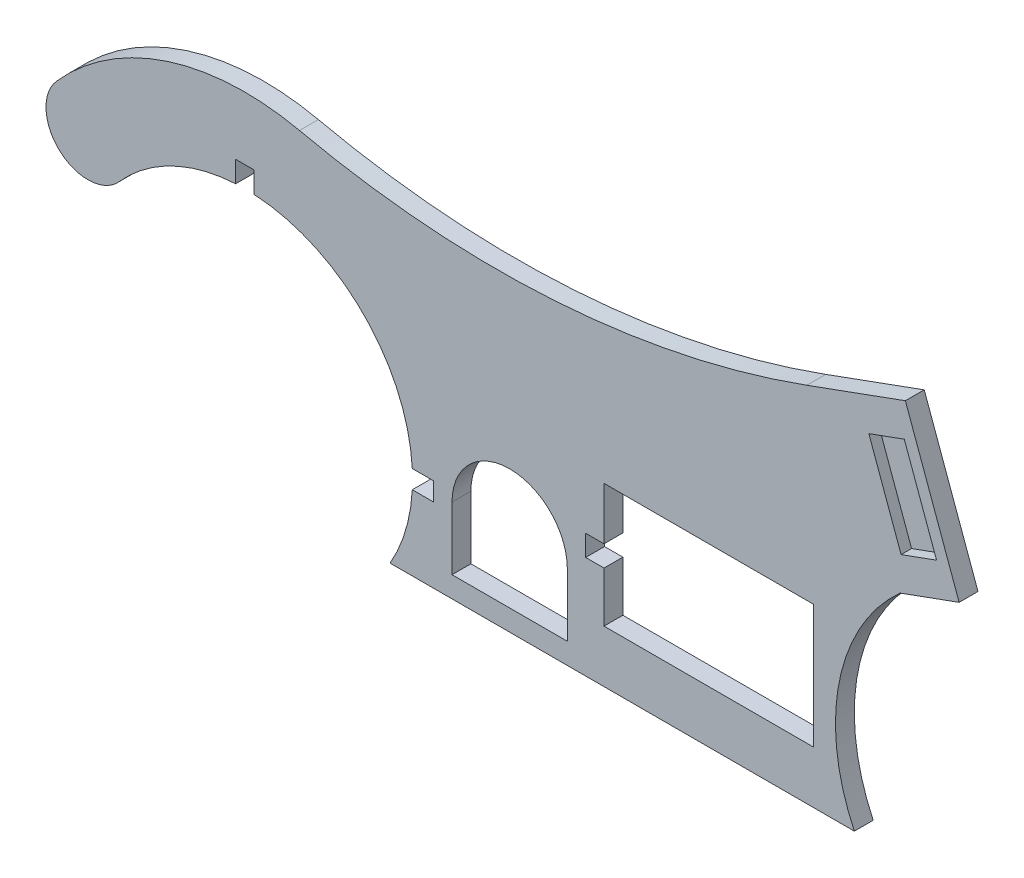
SolidWorks part; units mm, degrees
ref_plane "Спереди" through (0, 0, 0) normal (0, 0, 1) x (1, 0, 0)
ref_plane "Сверху" through (0, 0, 0) normal (0, 1, 0) x (1, 0, 0)
ref_plane "Справа" through (0, 0, 0) normal (1, 0, 0) x (0, 0, -1)
sketch "Sketch1" plane through (0, 0, 0) normal (0, 0, 1) x (1, 0, 0)
  line L0 (0, 0) -> (51.303, -140.9539)
  line L1 (-1000, 0) -> (49000, 0) construction
  line L2 (10.6418, 0) -> (119.8328, -300) construction
  line L3 (0, 0) -> (-93.9693, -34.202)
  line L4 (-491.6031, -380) -> (-48.6664, -380)
  line L5 (51.303, -140.9539) -> (-5.0785, -161.4751)
  circle A0 centre (119.8328, -300) radius 127.5 construction
  circle A1 centre (-630.1672, -300) radius 127.5 construction
  arc A3 (-491.6031, -380) -> (-749.9368, -193.9094) centre (-630.1672, -300) ccw
  arc A4 (-749.9368, -193.9094) -> (-809.8217, -140.864) centre (-779.8792, -167.3867) cw
  arc A5 (-809.8217, -140.864) -> (-578.031, -65.7313) centre (-630.1672, -300) cw
  arc A6 (-578.031, -65.7313) -> (-93.9693, -34.202) centre (-390.0044, 779.1478) ccw
  arc A7 (-48.6664, -380) -> (-5.0785, -161.4751) centre (119.8328, -300) cw
  dimension "D3" = 255
  dimension "D4" = 255
  dimension "D10" = 40
  dimension "D11" = 160
  dimension "D1" = 150
  dimension "D2" = 110
  dimension "D5" = 300
  dimension "D6" = 300
  dimension "D7" = 750
  dimension "D8" = 10
  dimension "D9" = 100
  dimension "D12" = 380
  dimension "D13" = 60
extrude "Boss-Extrude1" add sketch "Sketch1" along normal blind 18
sketch "Sketch2" plane through (0, 0, 18) normal (0, 0, 1) x (1, 0, 0)
  line L0 (-491.6031, -380) -> (-48.6664, -380) construction
  line L1 (-287.5083, -330) -> (-87.5083, -330)
  line L2 (-287.5083, -330) -> (-287.5083, -212)
  line L3 (-287.5083, -212) -> (-87.5083, -212)
  line L4 (-87.5083, -330) -> (-87.5083, -212)
  line L5 (-287.5083, -330) -> (-87.5083, -212) construction
  line L6 (-287.5083, -212) -> (-87.5083, -330) construction
  line L7 (-322.5083, -360) -> (-432.5083, -360)
  line L8 (-322.5083, -360) -> (-322.5083, -300)
  line L9 (-432.5083, -360) -> (-432.5083, -300)
  line L10 (-491.6031, -380) -> (-48.6664, -380) construction
  arc A0 (-432.5083, -300) -> (-322.5083, -300) centre (-377.5083, -300) cw
  point P0 (-187.5083, -271)
  dimension "D8" = 20
  dimension "D1" = 200
  dimension "D2" = 118
  dimension "D3" = 50
  dimension "D4" = 110
  dimension "D5" = 60
  dimension "D6" = 60
  dimension "D7" = 35
extrude "Cut-Extrude1" cut sketch "Sketch2" against normal through all
sketch "Sketch3" plane through (0, 0, 18) normal (0, 0, 1) x (1, 0, 0)
  line L0 (-1.0157, -32.295) -> (29.7661, -116.8674)
  line L1 (-1.0157, -32.295) -> (-34.8446, -44.6077)
  line L2 (29.7661, -116.8674) -> (-4.0628, -129.1801)
  line L3 (-34.8446, -44.6077) -> (-4.0628, -129.1801)
  line L5 (51.303, -140.9539) -> (0, 0) construction
  line L6 (0, 0) -> (-93.9693, -34.202) construction
  line L7 (-5.0785, -161.4751) -> (51.303, -140.9539) construction
  line L8 (-17.9302, -38.4514) -> (12.8516, -123.0237) construction
  dimension "D1" = 36
  dimension "D2" = 30
  dimension "D3" = 30
  dimension "D4" = 30
extrude "Cut-Extrude2" cut sketch "Sketch3" against normal blind 10
sketch "Sketch4" plane through (0, 0, 18) normal (0, 0, 1) x (1, 0, 0)
  line L0 (-630.1672, -300) -> (-630.1672, -12.7684) construction
  line L1 (-630.1672, -300) -> (-377.5083, -300) construction
  line L2 (-638.9172, -160) -> (-621.4172, -160)
  line L3 (-638.9172, -160) -> (-638.9172, -120)
  line L4 (-638.9172, -120) -> (-621.4172, -120)
  line L5 (-621.4172, -160) -> (-621.4172, -120)
  line L6 (-638.9172, -160) -> (-621.4172, -120) construction
  line L7 (-638.9172, -120) -> (-621.4172, -160) construction
  line L9 (-490.1672, -308.75) -> (-450.1672, -308.75)
  line L10 (-490.1672, -308.75) -> (-490.1672, -291.25)
  line L11 (-490.1672, -291.25) -> (-450.1672, -291.25)
  line L12 (-450.1672, -308.75) -> (-450.1672, -291.25)
  line L13 (-490.1672, -308.75) -> (-450.1672, -291.25) construction
  line L14 (-490.1672, -291.25) -> (-450.1672, -308.75) construction
  line L15 (-287.5083, -282) -> (-305.0083, -282)
  line L16 (-287.5083, -282) -> (-287.5083, -262)
  line L17 (-287.5083, -262) -> (-305.0083, -262)
  line L18 (-305.0083, -282) -> (-305.0083, -262)
  line L19 (-287.5083, -282) -> (-305.0083, -262) construction
  line L20 (-287.5083, -262) -> (-305.0083, -282) construction
  line L21 (-287.5083, -212) -> (-287.5083, -330) construction
  line L26 (-87.5083, -212) -> (-287.5083, -212) construction
  arc A0 (-491.6031, -380) -> (-749.9368, -193.9094) centre (-630.1672, -300) ccw construction
  point P4 (-630.1672, -140)
  point P11 (-302.7953, -255.8652)
  point P13 (-470.1672, -300)
  point P17 (-296.2583, -272)
  point P25 (-281.8442, -330)
  dimension "D1" = 17.5
  dimension "D2" = 40
  dimension "D3" = 17.5
  dimension "D4" = 40
  dimension "D5" = 60
  dimension "D6" = 17.5
  dimension "D7" = 20
extrude "Cut-Extrude3" cut sketch "Sketch4" against normal through all
